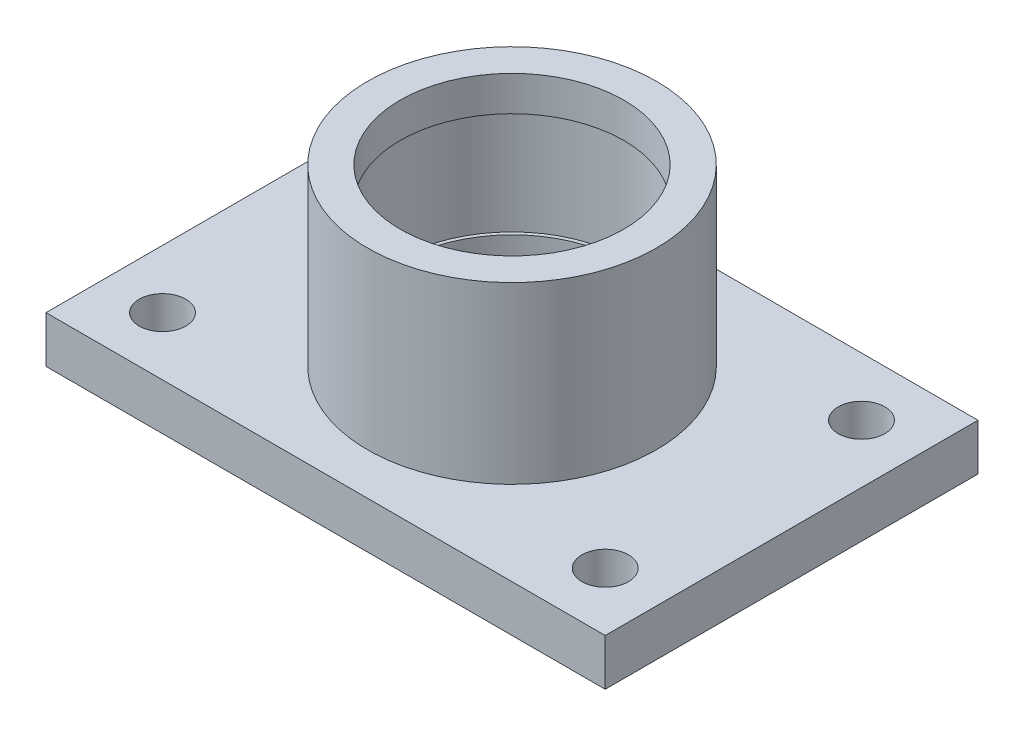
SolidWorks part; units mm, degrees
ref_plane "Front Plane" through (0, 0, 0) normal (0, 0, 1) x (1, 0, 0)
ref_plane "Top Plane" through (0, 0, 0) normal (0, 1, 0) x (1, 0, 0)
ref_plane "Right Plane" through (0, 0, 0) normal (1, 0, 0) x (0, 0, -1)
sketch "Sketch1" plane through (0, 0, 0) normal (0, 1, 0) x (1, 0, 0)
  line L1 (-120, -80) -> (120, -80)
  line L2 (-120, -80) -> (-120, 80)
  line L3 (-120, 80) -> (120, 80)
  line L4 (120, -80) -> (120, 80)
  dimension "D1" = 120
  dimension "D2" = 120
  dimension "D3" = 80
  dimension "D4" = 80
extrude "Boss-Extrude2" add sketch "Sketch1" along normal blind 20
sketch "Sketch3" plane through (0, 0, 0) normal (0, 0, 1) x (1, 0, 0)
  line L0 (0, -30.4276) -> (0, 119.5724) construction
  line L1 (48, 20) -> (48, 35)
  line L2 (-120, 20) -> (120, 20) construction
  line L3 (48, 35) -> (49.5, 35)
  line L4 (49.5, 35) -> (49.5, 80)
  line L5 (49.5, 80) -> (48, 80)
  line L6 (48, 80) -> (48, 95)
  line L7 (48, 95) -> (62, 95)
  line L8 (62, 95) -> (62, 20)
  line L9 (62, 20) -> (48, 20)
  dimension "D1" = 48
  dimension "D2" = 15
  dimension "D3" = 1.5
  dimension "D4" = 45
  dimension "D5" = 1.5
  dimension "D6" = 15
  dimension "D7" = 14
revolve "Revolve1" add sketch "Sketch3" angle 360 about L0
sketch "Sketch5" plane through (0, 0, 0) normal (0, -1, 0) x (1, 0, 0)
  line L0 (120, 80) -> (120, -80) construction
  line L1 (-120, 80) -> (120, 80) construction
  circle A0 centre (95, 55) radius 10
  circle A1 centre (-95, 55) radius 10
  circle A2 centre (-95, -55) radius 10
  circle A3 centre (95, -55) radius 10
  dimension "D3" = 20
  dimension "D1" = 25
  dimension "D2" = 25
  dimension "D4" = 2
  dimension "D5" = 2
extrude "Cut-Extrude2" cut sketch "Sketch5" against normal blind 20
sketch "Sketch6" plane through (0, 0, 0) normal (0, -1, 0) x (1, 0, 0)
  line L0 (-120, 80) -> (120, 80) construction
  line L1 (-110, 70) -> (110, 70)
  line L2 (-110, 70) -> (-110, -70)
  line L3 (-110, -70) -> (110, -70)
  line L4 (110, 70) -> (110, -70)
  line L5 (-120, -80) -> (-120, 80) construction
  line L6 (120, -80) -> (-120, -80) construction
  line L7 (120, 80) -> (120, -80) construction
  dimension "D1" = 10
  dimension "D2" = 10
  dimension "D3" = 10
  dimension "D4" = 10
sketch "Sketch8" plane through (0, 0, 0) normal (0, -1, 0) x (1, 0, 0)
extrude "Cut-Extrude3" cut sketch "Sketch6" against normal blind 3
sketch "Sketch9" plane through (0, 20, 0) normal (0, 1, 0) x (1, 0, 0)
  circle A0 centre (12, 0) radius 3
extrude "Cut-Extrude4" cut sketch "Sketch9" against normal blind 10
